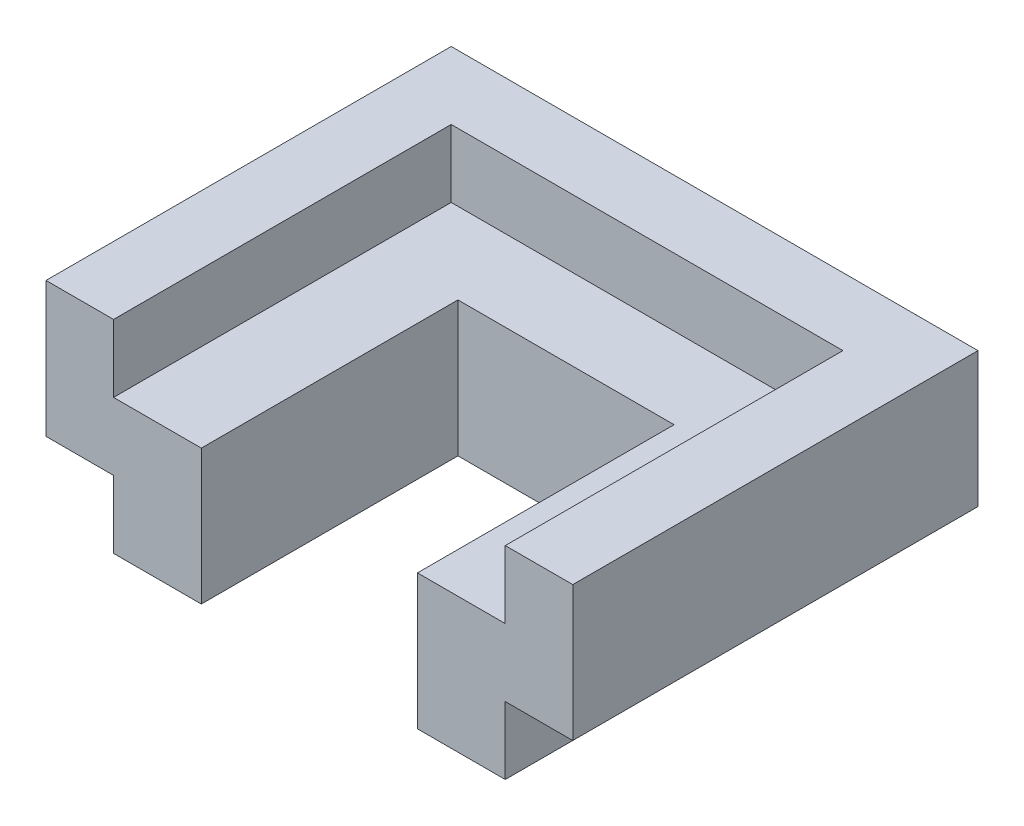
SolidWorks part; units mm, degrees
ref_plane "정면" through (0, 0, 0) normal (0, 0, 1) x (1, 0, 0)
ref_plane "윗면" through (0, 0, 0) normal (0, 1, 0) x (1, 0, 0)
ref_plane "우측면" through (0, 0, 0) normal (1, 0, 0) x (0, 0, -1)
sketch "스케치1" plane through (0, 0, 0) normal (0, 1, 0) x (1, 0, 0)
  line L0 (-14.5, 0) -> (-8, 0)
  line L1 (-8, 0) -> (-8, 19)
  line L2 (-8, 19) -> (8, 19)
  line L3 (8, 19) -> (8, 0)
  line L4 (8, 0) -> (14.5, 0)
  line L5 (14.5, 0) -> (14.5, 25)
  line L6 (14.5, 25) -> (-14.5, 25)
  line L7 (-14.5, 25) -> (-14.5, 0)
  dimension "D1" = 29
  dimension "D2" = 16
  dimension "D3" = 6.5
  dimension "D4" = 8
  dimension "D5" = 6
  dimension "D6" = 19
extrude "보스-돌출1" add sketch "스케치1" along normal blind 10
sketch "스케치2" plane through (0, 10, 0) normal (0, 1, 0) x (1, 0, 0)
  line L0 (-8, 0) -> (-19.5, 0)
  line L1 (-19.5, 0) -> (-19.5, 30)
  line L2 (-19.5, 30) -> (19.5, 30)
  line L3 (19.5, 30) -> (19.5, 0)
  line L4 (19.5, 0) -> (8, 0)
  line L5 (8, 0) -> (8, 19)
  line L6 (8, 19) -> (-8, 19)
  line L7 (-8, 19) -> (-8, 0)
  line L8 (14.5, 25) -> (-14.5, 25) construction
  dimension "D1" = 39
  dimension "D2" = 19.5
  dimension "D3" = 5
extrude "보스-돌출2" add sketch "스케치2" along normal blind 5 and the other way blind 5
sketch "스케치3" plane through (0, 15, 0) normal (0, 1, 0) x (1, 0, 0)
  line L0 (19.5, 30) -> (-19.5, 30) construction
  line L1 (14.5, -25) -> (-14.5, -25)
  line L2 (14.5, -25) -> (14.5, 25)
  line L3 (14.5, 25) -> (-14.5, 25)
  line L4 (-14.5, -25) -> (-14.5, 25)
  line L5 (14.5, -25) -> (-14.5, 25) construction
  line L6 (14.5, 25) -> (-14.5, -25) construction
  point P0 (0, 0)
  dimension "D1" = 5
  dimension "D2" = 29
extrude "컷-돌출2" cut sketch "스케치3" against normal blind 5
